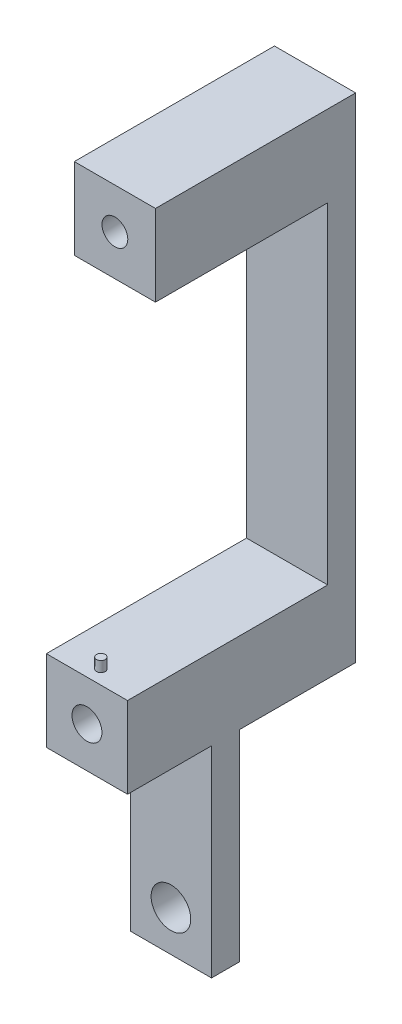
SolidWorks part; units mm, degrees
ref_plane "Front Plane" through (0, 0, 0) normal (0, 0, 1) x (1, 0, 0)
ref_plane "Top Plane" through (0, 0, 0) normal (0, 1, 0) x (1, 0, 0)
ref_plane "Right Plane" through (0, 0, 0) normal (1, 0, 0) x (0, 0, -1)
sketch "Sketch1" plane through (0, 0, 0) normal (0, 0, 1) x (1, 0, 0)
  line L1 (0, 0) -> (13.843, 0)
  line L2 (0, 0) -> (0, 48.133)
  line L3 (0, 48.133) -> (13.843, 48.133)
  line L4 (13.843, 0) -> (13.843, 48.133)
  dimension "D1" = 48.133
  dimension "D2" = 13.843
extrude "Boss-Extrude1" add sketch "Sketch1" along normal blind 4.7625
sketch "Sketch2" plane through (0, 0, 0) normal (0, 0, -1) x (-1, 0, 0)
  line L0 (0, 0) -> (-13.843, 0) construction
  circle A0 centre (-6.9215, 6.9215) radius 3.3782
  point P2 (0, 0)
  point P5 (-6.9215, 0)
  dimension "D1" = 6.7564
  dimension "D2" = 6.9215
extrude "Cut-Extrude1" cut sketch "Sketch2" against normal through all
sketch "Sketch3" plane through (0, 0, 4.7625) normal (0, 0, 1) x (1, 0, 0)
  line L0 (13.843, 0) -> (13.843, 48.133) construction
  line L1 (0, 48.133) -> (13.843, 48.133)
  line L2 (0, 48.133) -> (0, 34.29)
  line L3 (0, 34.29) -> (13.843, 34.29)
  line L4 (13.843, 48.133) -> (13.843, 34.29)
  dimension "D1" = 13.843
extrude "Boss-Extrude2" add sketch "Sketch3" along normal blind 14.3192
sketch "Sketch6" plane through (0, 0, 0) normal (0, 0, -1) x (-1, 0, 0)
  line L0 (0, 48.133) -> (0, 0) construction
  line L1 (-13.843, 48.133) -> (0, 48.133)
  line L2 (-13.843, 48.133) -> (-13.843, 34.29)
  line L3 (-13.843, 34.29) -> (0, 34.29)
  line L4 (0, 48.133) -> (0, 34.29)
  line L9 (0, 34.29) -> (-13.843, 34.29) construction
  point P7 (-98.1239, 44.7031)
  point P10 (0, 0)
  point P14 (0, 0)
extrude "Boss-Extrude3" add sketch "Sketch6" along normal blind 19.812
sketch "Sketch4" plane through (0, 0, 0) normal (0, 0, -1) x (-1, 0, 0)
  line L1 (-13.843, 48.133) -> (0, 48.133) construction
  circle A0 centre (-6.9215, 41.2115) radius 2.5527
  point P4 (0, 0)
  point P7 (-6.9215, 48.133)
  dimension "D1" = 5.1054
  dimension "D2" = 6.9215
extrude "Cut-Extrude2" cut sketch "Sketch4" against normal blind 27.0193
sketch "Sketch7" plane through (0, 0, -19.812) normal (0, 0, -1) x (-1, 0, 0)
  line L0 (-13.843, 34.29) -> (0, 34.29) construction
  line L1 (0, 34.29) -> (0, 48.133) construction
  circle A0 centre (-6.9215, 41.2115) radius 4.8641
  point P2 (0, 0)
  point P5 (-6.9215, 34.29)
  point P6 (0, 0)
  point P9 (0, 41.2115)
  dimension "D1" = 9.7282
extrude "Cut-Extrude3" cut sketch "Sketch7" against normal blind 19.812
sketch "Sketch8" plane through (0, 48.133, 0) normal (0, 1, 0) x (1, 0, 0)
  line L0 (0, -19.0817) -> (0, 19.812) construction
  line L1 (13.843, 19.812) -> (0, 19.812)
  line L2 (13.843, 19.812) -> (13.843, 15.0495)
  line L3 (13.843, 15.0495) -> (0, 15.0495)
  line L4 (0, 19.812) -> (0, 15.0495)
  dimension "D1" = 4.7625
extrude "Boss-Extrude4" add sketch "Sketch8" along normal blind 70.2818
sketch "Sketch9" plane through (0, 0, -15.0495) normal (0, 0, 1) x (1, 0, 0)
  line L0 (13.843, 118.4148) -> (13.843, 48.133) construction
  line L1 (0, 118.4148) -> (13.843, 118.4148)
  line L2 (0, 118.4148) -> (0, 104.5718)
  line L3 (0, 104.5718) -> (13.843, 104.5718)
  line L4 (13.843, 118.4148) -> (13.843, 104.5718)
  dimension "D1" = 13.843
extrude "Boss-Extrude5" add sketch "Sketch9" along normal blind 29.3687
sketch "Sketch10" plane through (0, 0, -19.812) normal (0, 0, -1) x (-1, 0, 0)
  line L0 (-13.843, 118.4148) -> (0, 118.4148) construction
  circle A0 centre (-6.9215, 111.4933) radius 4.1275
  point P2 (0, 0)
  point P5 (-6.9215, 118.4148)
  dimension "D1" = 8.255
  dimension "D2" = 6.9215
extrude "Cut-Extrude4" cut sketch "Sketch10" against normal blind 7.62
sketch "Sketch11" plane through (0, 0, -12.192) normal (0, 0, -1) x (-1, 0, 0)
  circle A0 centre (-6.9215, 111.4933) radius 2.2
  circle A1 centre (-6.9215, 111.4933) radius 4.1275 construction
  dimension "D1" = 4.4
extrude "Cut-Extrude5" cut sketch "Sketch11" against normal through all
sketch "Sketch12" plane through (0, 48.133, 0) normal (0, 1, 0) x (1, 0, 0)
  line L0 (13.843, -19.0817) -> (0, -19.0817) construction
  circle A0 centre (6.9215, -16.7005) radius 0.7493
  point P4 (0, 0)
  point P5 (6.9215, -19.0817)
  dimension "D2" = 1.4986
  dimension "D1" = 2.3813
extrude "Boss-Extrude6" add sketch "Sketch12" along normal blind 1.778
